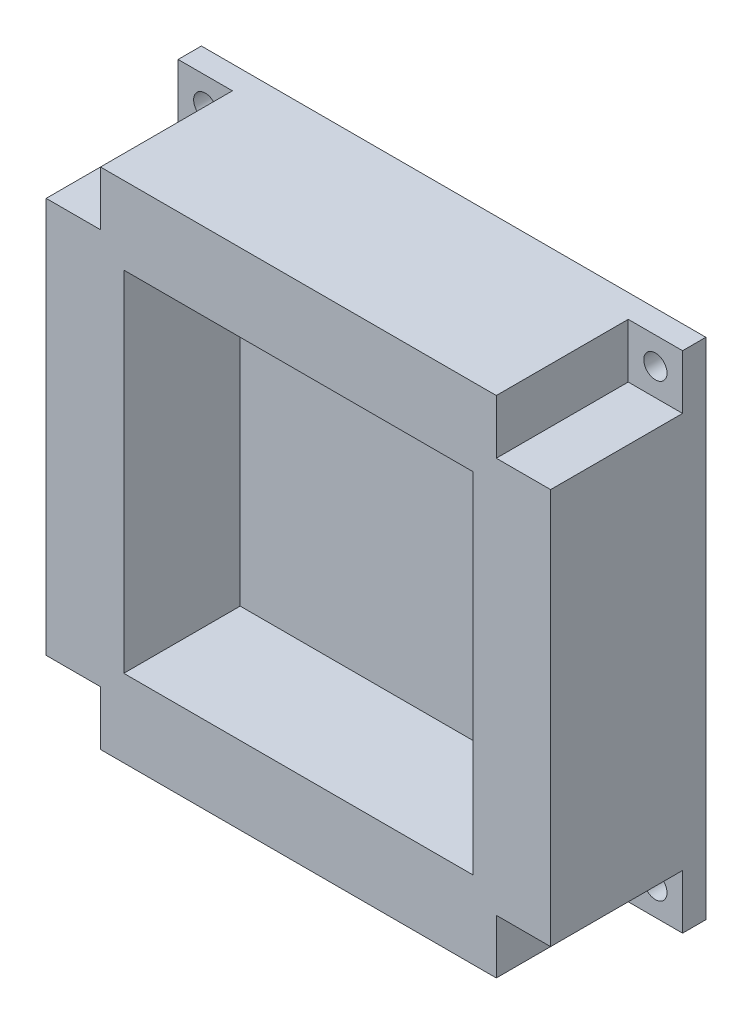
SolidWorks part; units mm, degrees
ref_plane "Спереди" through (0, 0, 0) normal (0, 0, 1) x (1, 0, 0)
ref_plane "Сверху" through (0, 0, 0) normal (0, 1, 0) x (1, 0, 0)
ref_plane "Справа" through (0, 0, 0) normal (1, 0, 0) x (0, 0, -1)
sketch "Эскиз1" plane through (0, 0, 0) normal (0, 0, 1) x (1, 0, 0)
  line L1 (-32.5, 32.5) -> (32.5, 32.5)
  line L2 (-32.5, 32.5) -> (-32.5, -32.5)
  line L3 (-32.5, -32.5) -> (32.5, -32.5)
  line L4 (32.5, 32.5) -> (32.5, -32.5)
  line L5 (-32.5, 32.5) -> (32.5, -32.5) construction
  line L6 (-32.5, -32.5) -> (32.5, 32.5) construction
  point P0 (0, 0)
  dimension "D1" = 65
  dimension "D2" = 65
extrude "Бобышка-Вытянуть4" add sketch "Эскиз1" along normal blind 20
sketch "Эскиз3" plane through (0, 0, 20) normal (0, 0, 1) x (1, 0, 0)
  line L1 (-22.5, 22.5) -> (22.5, 22.5)
  line L2 (-22.5, 22.5) -> (-22.5, -22.5)
  line L3 (-22.5, -22.5) -> (22.5, -22.5)
  line L4 (22.5, 22.5) -> (22.5, -22.5)
  line L5 (-22.5, 22.5) -> (22.5, -22.5) construction
  line L6 (-22.5, -22.5) -> (22.5, 22.5) construction
  point P0 (0, 0)
  dimension "D1" = 45
  dimension "D2" = 45
extrude "Вырез-Вытянуть1" cut sketch "Эскиз3" against normal blind 15
sketch "Эскиз4" plane through (0, 0, 20) normal (0, 0, 1) x (1, 0, 0)
  line L1 (-32.5, 32.5) -> (-25.5, 32.5)
  line L2 (-32.5, 32.5) -> (-32.5, 25.5)
  line L3 (-32.5, 25.5) -> (-25.5, 25.5)
  line L4 (-25.5, 32.5) -> (-25.5, 25.5)
  dimension "D1" = 7
  dimension "D2" = 7
extrude "Вырез-Вытянуть2" cut sketch "Эскиз4" against normal blind 17
pattern_circular "Круговой массив1" count 4 over 360 about axis through (0, 0, 0) along (0, 0, 1) of "Вырез-Вытянуть2"
sketch "Эскиз5" plane through (0, 0, 3) normal (0, 0, 1) x (1, 0, 0)
  line L0 (-25.5, 25.5) -> (-25.5, 32.5) construction
  line L1 (-32.5, 25.5) -> (-25.5, 25.5) construction
  circle A0 centre (-29, 29) radius 1.5
  point P0 (-29, 29)
  dimension "D3" = 3
  dimension "D1" = 3.5
  dimension "D2" = 3.5
extrude "Вырез-Вытянуть3" cut sketch "Эскиз5" against normal blind 3
pattern_circular "Круговой массив2" count 4 over 360 about axis through (0, 0, 0) along (0, 0, 1) of "Вырез-Вытянуть3"
